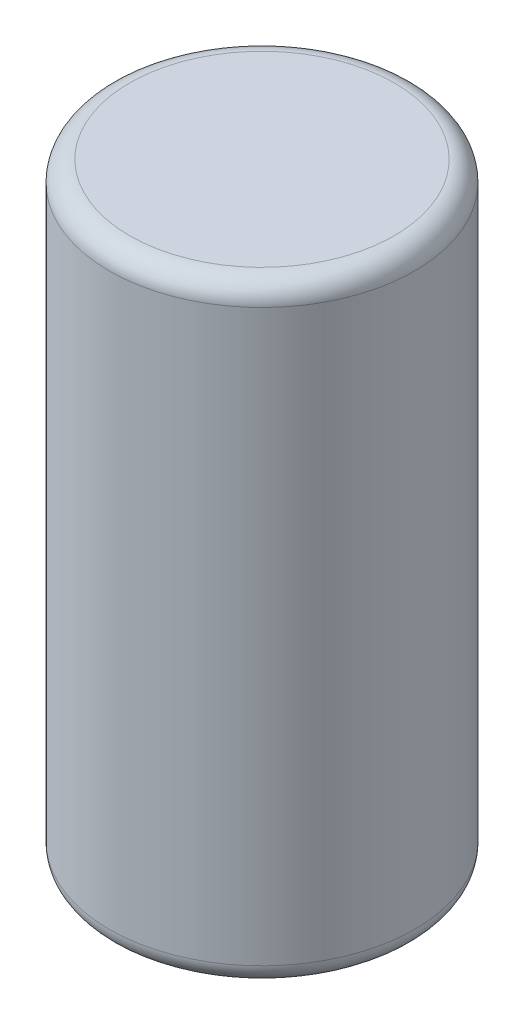
SolidWorks part; units mm, degrees
material "Alliage de magnésium"
ref_plane "Plan de face" through (0, 0, 0) normal (0, 0, 1) x (1, 0, 0)
ref_plane "Plan de dessus" through (0, 0, 0) normal (0, 1, 0) x (1, 0, 0)
ref_plane "Plan de droite" through (0, 0, 0) normal (1, 0, 0) x (0, 0, -1)
sketch "Esquisse1" plane through (0, 0, 0) normal (0, 1, 0) x (1, 0, 0)
  circle A0 centre (0, 0) radius 1.5
  dimension "D1" = 3
extrude "Boss.-Extru.1" add sketch "Esquisse1" along normal blind 6
fillet "Congé1" radius 0.2 2 edges at (0, 0, 1.5) (0, 6, 1.5)
